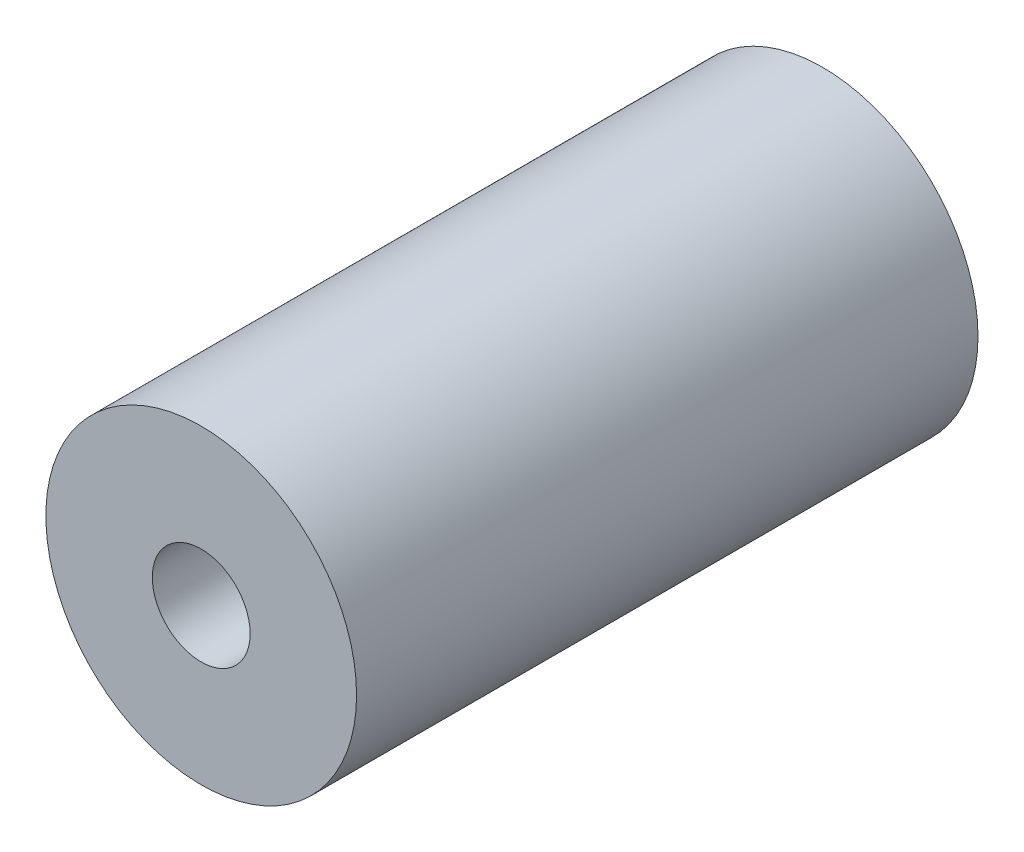
SolidWorks part; units mm, degrees
material "7079 Alloy"
ref_plane "Front Plane" through (0, 0, 0) normal (0, 0, 1) x (1, 0, 0)
ref_plane "Top Plane" through (0, 0, 0) normal (0, 1, 0) x (1, 0, 0)
ref_plane "Right Plane" through (0, 0, 0) normal (1, 0, 0) x (0, 0, -1)
sketch "Sketch1" plane through (0, 0, 0) normal (0, 0, 1) x (1, 0, 0)
  circle A0 centre (0, 0) radius 2
  circle A1 centre (0, 0) radius 6.35
  dimension "D1" = 4
  dimension "D2" = 12.7
extrude "Boss-Extrude1" add sketch "Sketch1" along normal blind 25.4
